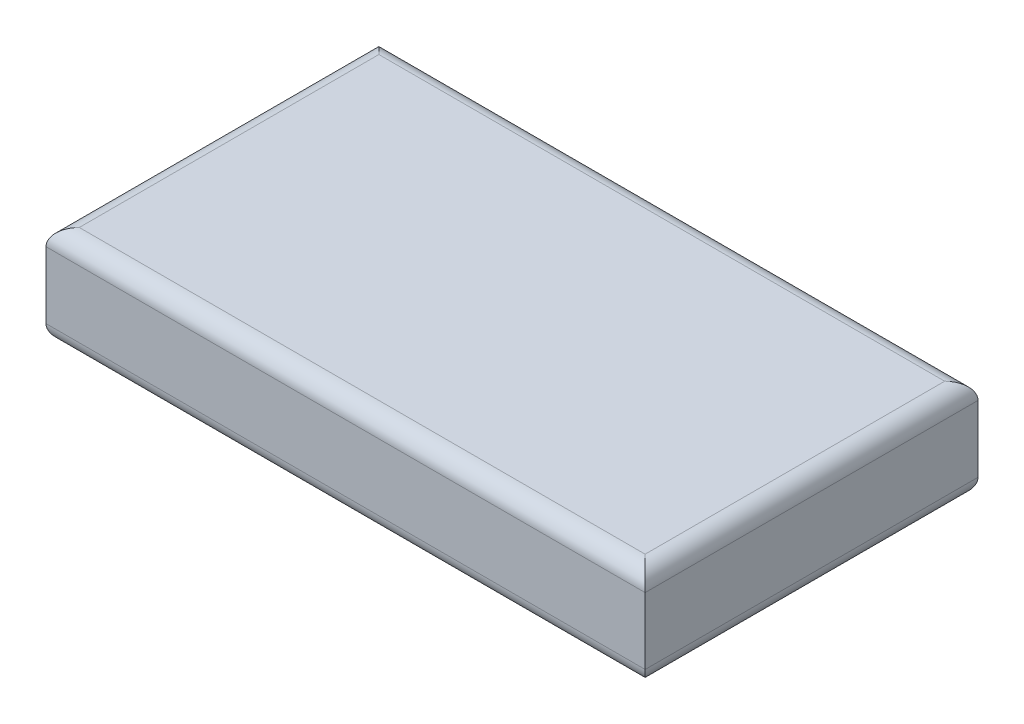
SolidWorks part; units mm, degrees
ref_plane "Front Plane" through (0, 0, 0) normal (0, 0, 1) x (1, 0, 0)
ref_plane "Top Plane" through (0, 0, 0) normal (0, 1, 0) x (1, 0, 0)
ref_plane "Right Plane" through (0, 0, 0) normal (1, 0, 0) x (0, 0, -1)
sketch "Sketch1" plane through (0, 0, 0) normal (0, 1, 0) x (1, 0, 0)
  line L1 (-18, 10) -> (18, 10)
  line L2 (-18, 10) -> (-18, -10)
  line L3 (-18, -10) -> (18, -10)
  line L4 (18, 10) -> (18, -10)
  line L5 (-18, 10) -> (18, -10) construction
  line L6 (-18, -10) -> (18, 10) construction
  point P0 (0, 0)
  dimension "D1" = 36
  dimension "D2" = 20
extrude "Boss-Extrude1" add sketch "Sketch1" along normal blind 6
fillet "Fillet1" radius 1 8 edges at (0, 0, -10) (-18, 0, 0) (0, 0, 10) (18, 0, 0) (0, 6, 10) (-18, 6, 0) (0, 6, -10) (18, 6, 0)
